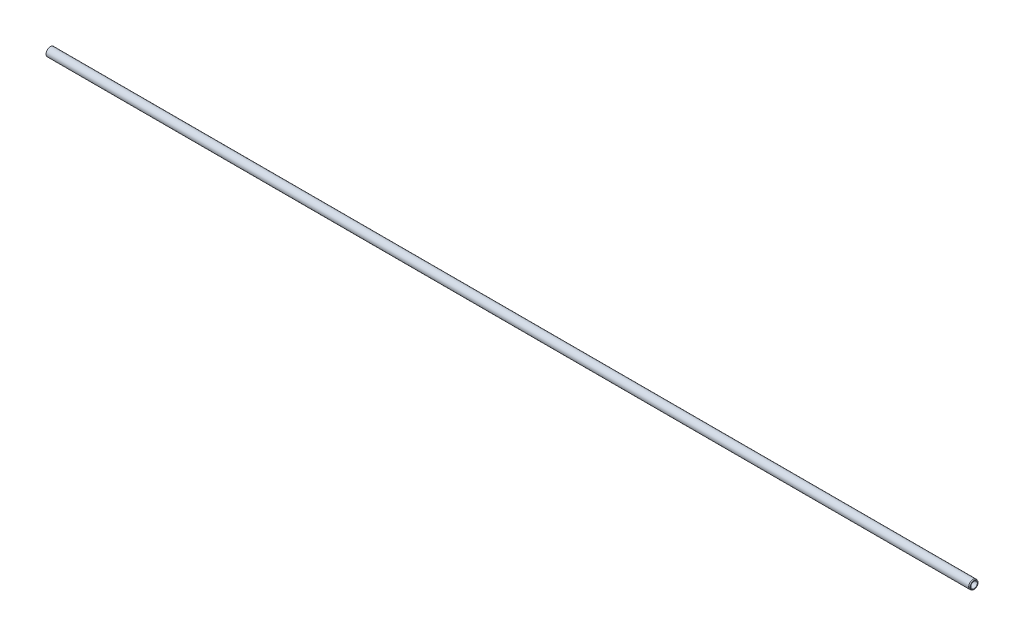
SolidWorks part; units mm, degrees
ref_plane "Front" through (0, 0, 0) normal (0, 0, 1) x (1, 0, 0)
ref_plane "Top" through (0, 0, 0) normal (0, 1, 0) x (1, 0, 0)
ref_plane "Right" through (0, 0, 0) normal (1, 0, 0) x (0, 0, -1)
sketch "Sketch1" plane through (0, 0, 0) normal (0, 0, 1) x (1, 0, 0)
  line L0 (0, 0) -> (1352.4571, 0) construction
  line L1 (0, 10) -> (0, 7.5)
  line L2 (0, 7.5) -> (2140, 7.5)
  line L4 (0, 10) -> (2137.5, 10)
  line L6 (2137.5, 10) -> (2140, 9.0901)
  line L7 (2140, 9.0901) -> (2140, 7.5)
  dimension "D1" = 20
  dimension "D2" = 15
  dimension "D3" = 20
  dimension "D4" = 2.5
  dimension "D6" = 2140
revolve "Base-Revolve" add sketch "Sketch1" angle 360 about L0
